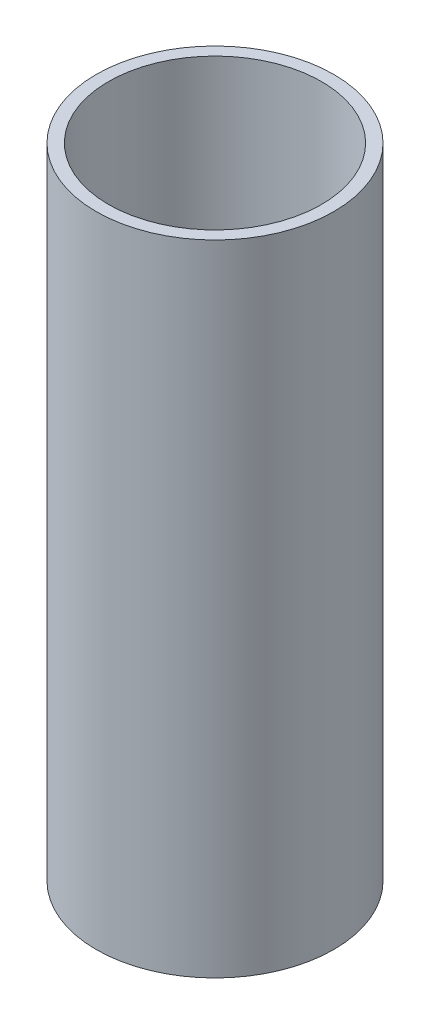
SolidWorks part; units mm, degrees
ref_plane "Front" through (0, 0, 0) normal (0, 0, 1) x (1, 0, 0)
ref_plane "Top" through (0, 0, 0) normal (0, 1, 0) x (1, 0, 0)
ref_plane "Right" through (0, 0, 0) normal (1, 0, 0) x (0, 0, -1)
sketch "Sketch1" plane through (0, 0, 0) normal (0, 1, 0) x (1, 0, 0)
  circle A0 centre (0, 0) radius 50.8
  dimension "D1" = 101.6
extrude "Extrude-Thin1" add sketch "Sketch1" along normal blind 304.8 thin
